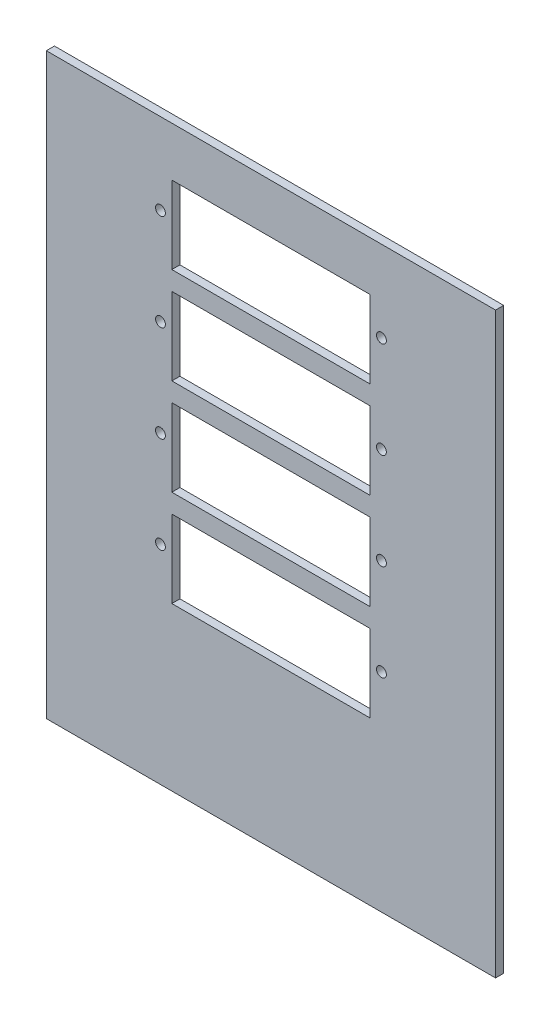
SolidWorks part; units mm, degrees
ref_plane "Plan de face" through (0, 0, 0) normal (0, 0, 1) x (1, 0, 0)
ref_plane "Plan de dessus" through (0, 0, 0) normal (0, 1, 0) x (1, 0, 0)
ref_plane "Plan de droite" through (0, 0, 0) normal (1, 0, 0) x (0, 0, -1)
sketch "Esquisse1" plane through (0, 0, 0) normal (0, 0, 1) x (1, 0, 0)
  line L1 (-161.8321, 173.5369) -> (71.1679, 173.5369)
  line L2 (-161.8321, 173.5369) -> (-161.8321, -126.4631)
  line L3 (-161.8321, -126.4631) -> (71.1679, -126.4631)
  line L4 (71.1679, 173.5369) -> (71.1679, -126.4631)
  dimension "D1" = 300
  dimension "D2" = 233
extrude "Boss.-Extru.1" add sketch "Esquisse1" along normal blind 4.2
sketch "Esquisse2" plane through (0, 0, 4.2) normal (0, 0, 1) x (1, 0, 0)
  line L1 (-96.7321, -2.0231) -> (6.0679, -2.0231)
  line L2 (-96.7321, -2.0231) -> (-96.7321, -42.2231)
  line L3 (-96.7321, -42.2231) -> (6.0679, -42.2231)
  line L4 (6.0679, -2.0231) -> (6.0679, -42.2231)
  line L5 (71.1679, -126.4631) -> (71.1679, 173.5369) construction
  line L6 (-96.7321, 47.9769) -> (6.0679, 47.9769)
  line L7 (-96.7321, 47.9769) -> (-96.7321, 7.7769)
  line L8 (-96.7321, 7.7769) -> (6.0679, 7.7769)
  line L9 (6.0679, 47.9769) -> (6.0679, 7.7769)
  line L10 (-96.7321, 97.9769) -> (6.0679, 97.9769)
  line L11 (-96.7321, 97.9769) -> (-96.7321, 57.7769)
  line L12 (-96.7321, 57.7769) -> (6.0679, 57.7769)
  line L13 (6.0679, 97.9769) -> (6.0679, 57.7769)
  line L14 (-96.7321, 147.9769) -> (6.0679, 147.9769)
  line L15 (-96.7321, 147.9769) -> (-96.7321, 107.7769)
  line L16 (-96.7321, 107.7769) -> (6.0679, 107.7769)
  line L17 (6.0679, 147.9769) -> (6.0679, 107.7769)
  line L18 (-161.8321, -126.4631) -> (71.1679, -126.4631) construction
  circle A6 centre (-102.6321, 131.4269) radius 2.55
  circle A9 centre (11.9679, 131.4269) radius 2.55
  circle A10 centre (-102.6321, 81.4269) radius 2.55
  circle A11 centre (11.9679, 81.4269) radius 2.55
  circle A12 centre (-102.6321, 31.4269) radius 2.55
  circle A13 centre (11.9679, 31.4269) radius 2.55
  circle A14 centre (-102.6321, -18.5731) radius 2.55
  circle A15 centre (11.9679, -18.5731) radius 2.55
  dimension "D17" = 5.9
  dimension "D20" = 16.55
  dimension "D23" = 50
  dimension "D24" = 50
  dimension "D35" = 5.1
  dimension "D45" = 5.1
  dimension "D47" = 5.1
  dimension "D51" = 5.1
  dimension "D54" = 5.1
  dimension "D56" = 5.1
  dimension "D61" = 5.1
  dimension "D63" = 5.1
  dimension "D1" = 102.8
  dimension "D2" = 40.2
  dimension "D3" = 65.1
  dimension "D4" = 0
  dimension "D5" = 9.8
  dimension "D6" = 40.2
  dimension "D7" = 102.8
  dimension "D8" = 40.2
  dimension "D9" = 102.8
  dimension "D10" = 40.2
  dimension "D11" = 102.8
  dimension "D12" = 0
  dimension "D13" = 9.8
  dimension "D14" = 9.8
  dimension "D15" = 0
  dimension "D16" = 84.24
  dimension "D18" = 50
  dimension "D19" = 50
  dimension "D21" = 23.65
  dimension "D22" = 50
  dimension "D25" = 50
  dimension "D26" = 107.89
  dimension "D36" = 5.9
  dimension "D41" = 107.89
  dimension "D44" = 5.9
  dimension "D48" = 5.9
  dimension "D52" = 5.9
  dimension "D53" = 5.9
  dimension "D59" = 5.9
  dimension "D62" = 5.9
extrude "Enlèv. mat.-Extru.1" cut sketch "Esquisse2" against normal through all and the other way through all
